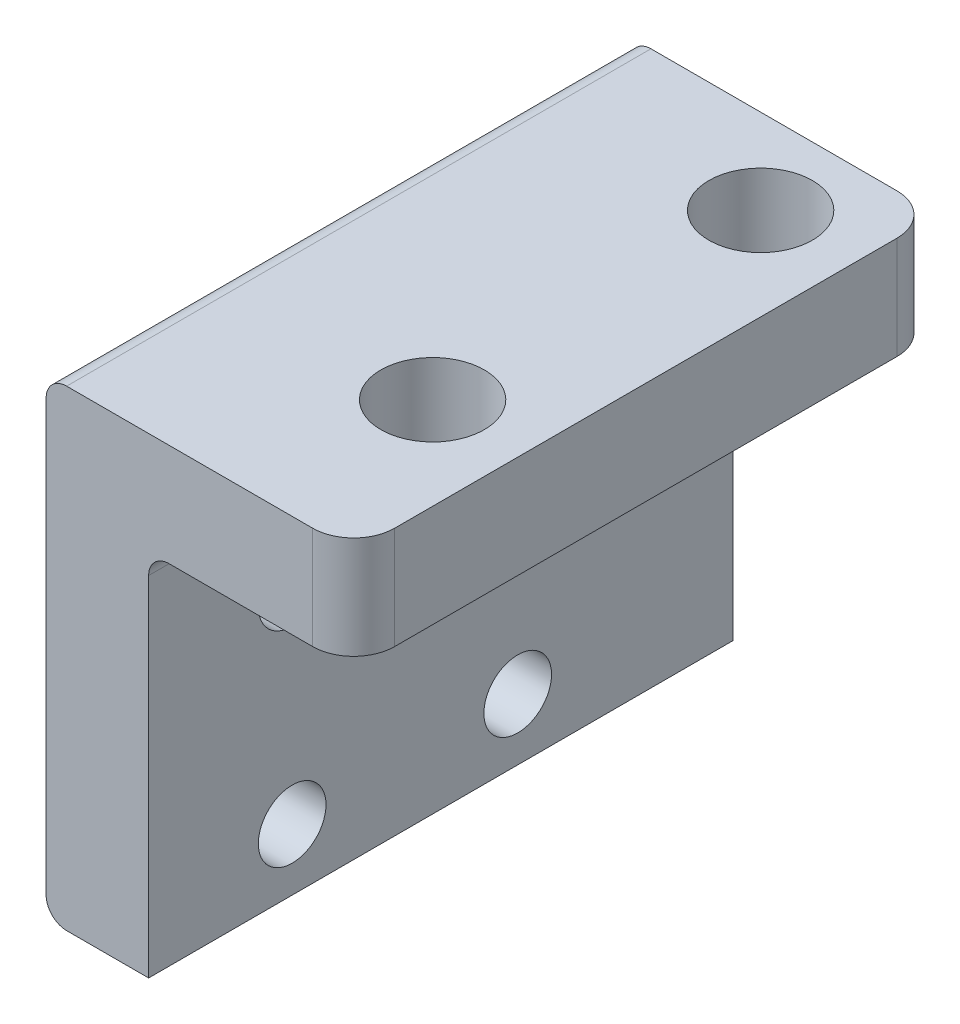
SolidWorks part; units mm, degrees
material "6063-T5"
ref_plane "前视基准面" through (0, 0, 0) normal (0, 0, 1) x (1, 0, 0)
ref_plane "上视基准面" through (0, 0, 0) normal (0, 1, 0) x (1, 0, 0)
ref_plane "右视基准面" through (0, 0, 0) normal (1, 0, 0) x (0, 0, -1)
other "Configuration Table"
sketch "草图1" plane through (0, 0, 0) normal (0, 0, 1) x (1, 0, 0)
  line L0 (0, 0) -> (10, 0)
  line L1 (10, 0) -> (10, 5)
  line L2 (10, 5) -> (-5, 5)
  line L3 (-5, 5) -> (-5, -18)
  line L4 (-5, -18) -> (0, -18)
  line L5 (0, -18) -> (0, 0)
  dimension "D1" = 5
  dimension "D2" = 15
  dimension "D3" = 23
extrude "凸台-拉伸1" add sketch "草图1" along normal blind 28.5
sketch "草图2" plane through (0, 0, 0) normal (1, 0, 0) x (0, 0, -1)
  line L0 (-28.5, -18) -> (-28.5, 0) construction
  line L1 (-21.5, -15) -> (-10.5, -15) construction
  line L2 (-21.5, -15) -> (-21.5, -5) construction
  line L3 (-21.5, -5) -> (-10.5, -5) construction
  line L4 (-10.5, -15) -> (-10.5, -5) construction
  line L5 (-21.5, -15) -> (-10.5, -5) construction
  line L6 (-21.5, -5) -> (-10.5, -15) construction
  line L7 (-28.5, -18) -> (0, -18) construction
  point P0 (-16, -10)
  dimension "D1" = 7
  dimension "D2" = 10
  dimension "D3" = 3
  dimension "D4" = 11
hole_wizard "M4 螺纹孔1" positions "3D草图1" profile "草图3" tap size "M4" standard "GB" end condition through all
sketch3d "3D草图1"
  point P0 (0, -5, 21.5)
  point P3 (0, -15, 21.5)
  point P6 (0, -15, 10.5)
  point P9 (0, -5, 10.5)
sketch "草图3" plane through (0, -5, 21.5) normal (0, 1, 0) x (0, 0, -1)
  line L0 (0, 0) -> (0, 5)
  line L1 (0, 5) -> (1.65, 5)
  line L2 (1.65, 5) -> (1.65, 0)
  line L5 (1.65, 0) -> (0, 0)
  line L11 (0, -6.35) -> (0, 107.95) construction
  dimension "通孔螺纹孔钻头直径" = 3.3
  dimension "通孔螺纹孔钻头深度" = 5
cosmetic thread "孔螺蚊线1" parameters "D2"=4
cosmetic thread "孔螺蚊线2" parameters "D2"=4
cosmetic thread "孔螺蚊线3" parameters "D2"=4
cosmetic thread "孔螺蚊线4" parameters "D2"=4
fillet "圆角1" radius 2 2 edges at (10, 2.5, 0) (10, 2.5, 28.5)
sketch "草图4" plane through (0, 5, 0) normal (0, 1, 0) x (1, 0, 0)
  line L0 (10, -26.5) -> (10, -2) construction
  line L1 (8, -28.5) -> (-5, -28.5) construction
  circle A0 centre (5.5, -20.15) radius 2.525
  circle A1 centre (5.5, -4.15) radius 2.525
  dimension "D1" = 5.05
  dimension "D2" = 8.35
  dimension "D3" = 4.5
  dimension "D4" = 16
  dimension "D5" = 4.5
extrude "切除-拉伸1" cut sketch "草图4" against normal blind 10
fillet "圆角2" radius 1 3 edges at (0, 0, 14.25) (-5, -18, 14.25) (-5, 5, 14.25)
